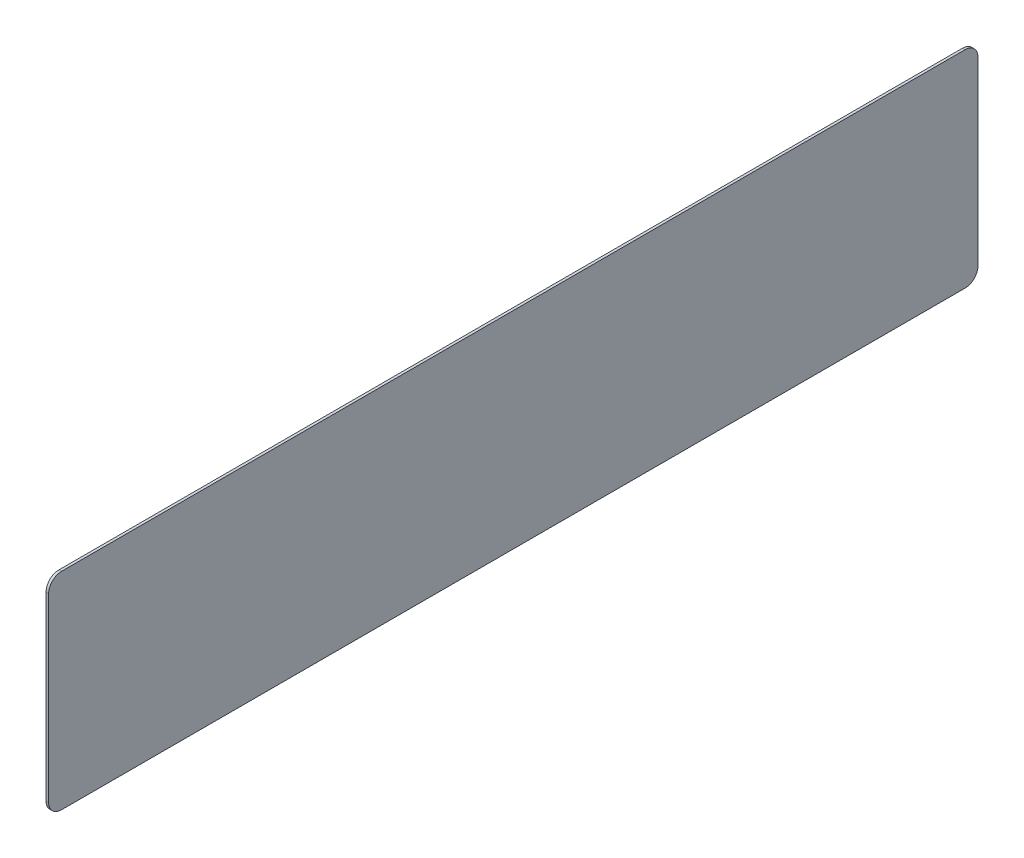
SolidWorks part; units mm, degrees
ref_plane "Front Plane" through (0, 0, 0) normal (0, 0, 1) x (1, 0, 0)
ref_plane "Top Plane" through (0, 0, 0) normal (0, 1, 0) x (1, 0, 0)
ref_plane "Right Plane" through (0, 0, 0) normal (1, 0, 0) x (0, 0, -1)
sketch "Sketch1" plane through (0, 0, 0) normal (1, 0, 0) x (0, 0, -1)
  line L1 (-90, -20) -> (90, -20)
  line L2 (-90, -20) -> (-90, 20)
  line L3 (-90, 20) -> (90, 20)
  line L4 (90, -20) -> (90, 20)
  line L5 (-90, -20) -> (90, 20) construction
  line L6 (-90, 20) -> (90, -20) construction
  point P0 (0, 0)
  dimension "D1" = 180
  dimension "D2" = 40
extrude "Boss-Extrude1" add sketch "Sketch1" along normal blind 0.5
fillet "Fillet1" radius 2.5 4 edges at (0.25, -20, -90) (0.25, 20, -90) (0.25, -20, 90) (0.25, 20, 90)
